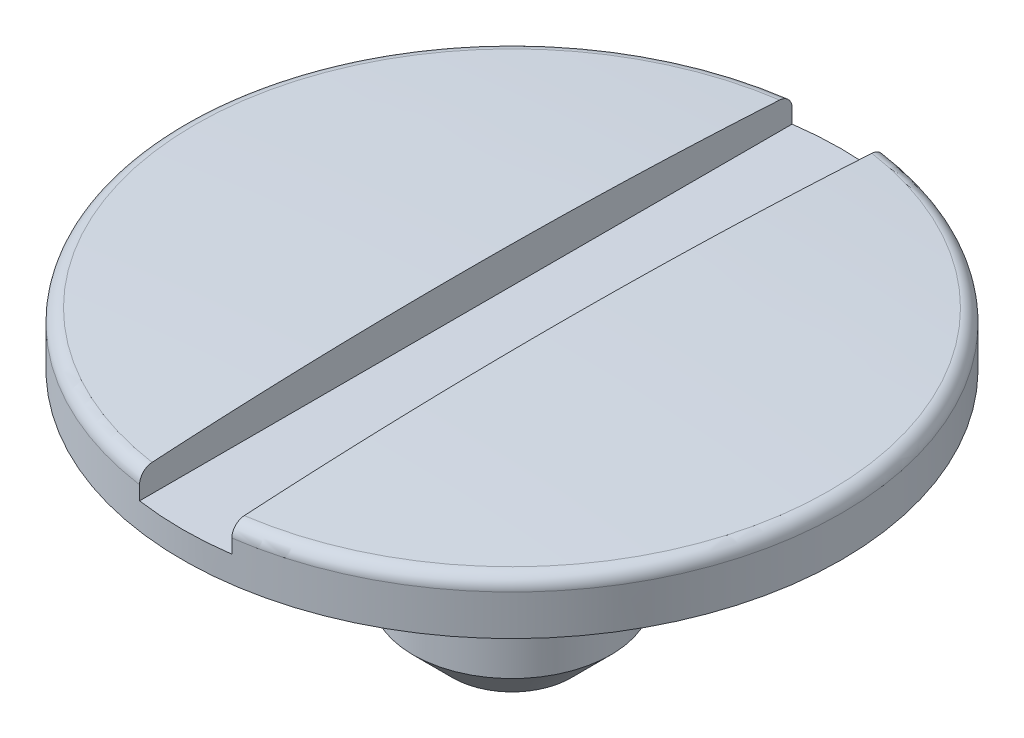
SolidWorks part; units mm, degrees
ref_plane "Alzado" through (0, 0, 0) normal (0, 0, 1) x (1, 0, 0)
ref_plane "Planta" through (0, 0, 0) normal (0, 1, 0) x (1, 0, 0)
ref_plane "Vista lateral" through (0, 0, 0) normal (1, 0, 0) x (0, 0, -1)
sketch "Sketch4" plane through (0, 0, 0) normal (0, 0, 1) x (1, 0, 0)
  line L0 (-848.3562, 0) -> (41569.4551, 0) construction
  line L1 (-848.2787, 0.2) -> (41569.5327, 0.2) construction
  line L2 (0, -848.3562) -> (0, 41569.4551) construction
  line L3 (1.25, -848.3562) -> (1.25, 41569.4551) construction
  line L4 (0, 0) -> (1.25, 0)
  line L5 (1.25, 0) -> (1.25, 0.2)
  line L6 (0, 0.2391) -> (0, 0)
  arc A1 (0, 0.2391) -> (1.25, 0.2) centre (0, -19.7609) cw
  point P8 (1.25, 0.2)
  dimension "D3" = 20
  dimension "D1" = 1.25
  dimension "D2" = 0.2
revolve "Revolve1" add sketch "Sketch4" angle 360 about L2
sketch "Sketch2" plane through (0, 0, 0) normal (0, 1, 0) x (1, 0, 0)
  circle A0 centre (0, 0) radius 0.375
  dimension "D1" = 0.75
extrude "Boss-Extrude2" add sketch "Sketch2" against normal blind 0.9
fillet "Fillet1" radius 0.05 1 edges at (1.25, 0.2, 0)
chamfer "Chamfer2" distance 0.15 angle 45 1 edges at (0, -0.9, 0.375)
sketch "Sketch3" plane through (0, 0, 0) normal (0, 0, 1) x (1, 0, 0)
  line L0 (0, -1000) -> (0, 49000) construction
  line L2 (-0.175, -999.9073) -> (-0.175, 49000.0927) construction
  line L3 (-1000, 0) -> (49000, 0) construction
  line L4 (-1000.8273, 0.1) -> (48999.1727, 0.1) construction
  line L5 (-0.175, 0.35) -> (0, 0.35)
  line L6 (-0.175, 0.35) -> (-0.175, 0.1)
  line L7 (0.175, 0.1) -> (0, 0.1)
  line L8 (-0.175, 0.1) -> (0, 0.1)
  line L9 (0.175, 0.35) -> (0.175, 0.1)
  line L10 (0.175, 0.35) -> (0, 0.35)
  dimension "D1" = 0.1
  dimension "D2" = 0.175
extrude "Cut-Extrude1" cut sketch "Sketch3" against normal through all both and the other way through all
